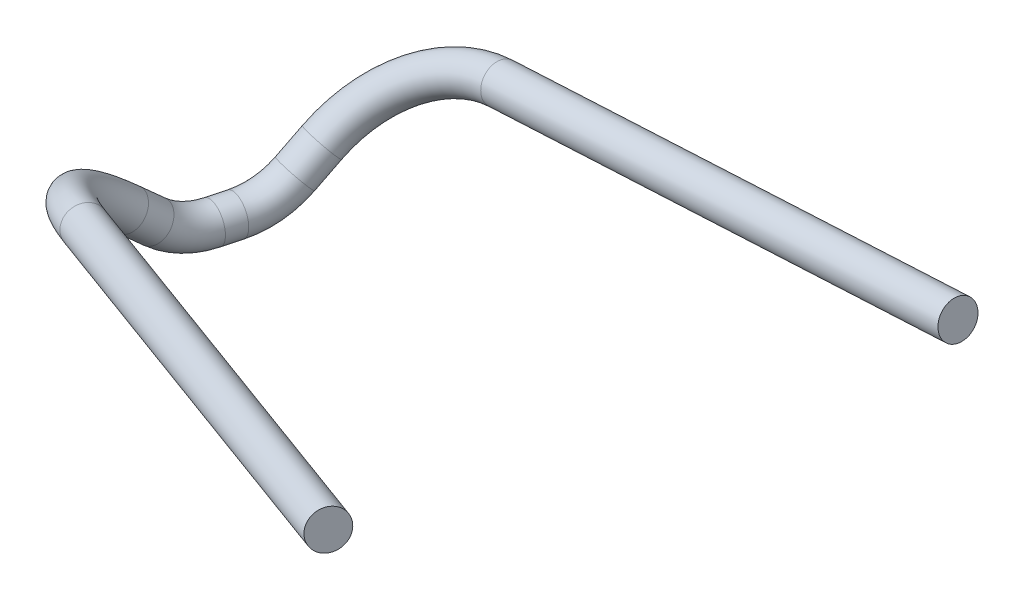
SolidWorks part; units mm, degrees
ref_plane "Front Plane" through (0, 0, 0) normal (0, 0, 1) x (1, 0, 0)
ref_plane "Top Plane" through (0, 0, 0) normal (0, 1, 0) x (1, 0, 0)
ref_plane "Right Plane" through (0, 0, 0) normal (1, 0, 0) x (0, 0, -1)
sketch3d "3DSketch1"
  line L0 (-98.1157, -7.2801, 68.2928) -> (-97.8827, -6.4921, 67.4233)
  line L5 (-98.6271, -8.023, 70.2016) -> (-98.8283, -8.023, 70.9525)
  line L14 (-96.7608, -3.4703, 78.2527) -> (-78.0843, -0.523, 86.9619)
  line L16 (-99.5482, -6.6026, 73.6393) -> (-99.3285, -7.3177, 72.8191)
  line L17 (-93.1434, -3.3118, 64.8599) -> (-72.6491, -0.523, 66.6774)
  arc A0 (-98.8283, -8.023, 70.9525) -> (-99.3285, -7.3177, 72.8191) centre (-98.8283, -5.023, 70.9525) ccw
  arc A1 (-98.6271, -8.023, 70.2016) -> (-98.1157, -7.2801, 68.2928) centre (-98.6271, -5.023, 70.2016) ccw
  arc A2 (-96.7608, -3.4703, 78.2527) -> (-99.5482, -6.6026, 73.6393) centre (-94.7207, -6.6122, 74.9412) ccw
  arc A3 (-93.1434, -3.3118, 64.8599) -> (-97.8827, -6.4921, 67.4233) centre (-93.0433, -6.5365, 68.6798) ccw
  point P2 (-99.1117, -8.023, 72.0101)
  point P4 (-101.7261, -5.023, 70.1761)
  point P7 (-98.3353, -8.023, 69.1124)
  point P9 (-95.7293, -5.023, 70.9781)
  point P12 (-100.3375, -4.0347, 76.5848)
  point P14 (-95.5663, -10.4367, 78.0488)
  point P17 (-97.1018, -3.8504, 64.5089)
  point P19 (-93.8387, -2.7748, 71.8762)
  dimension "D1" = 3
  dimension "D2" = 5
sweep "Sweep1" add path "3DSketch1" circular profile diameter 1.5 parameters "D3"=1.5
